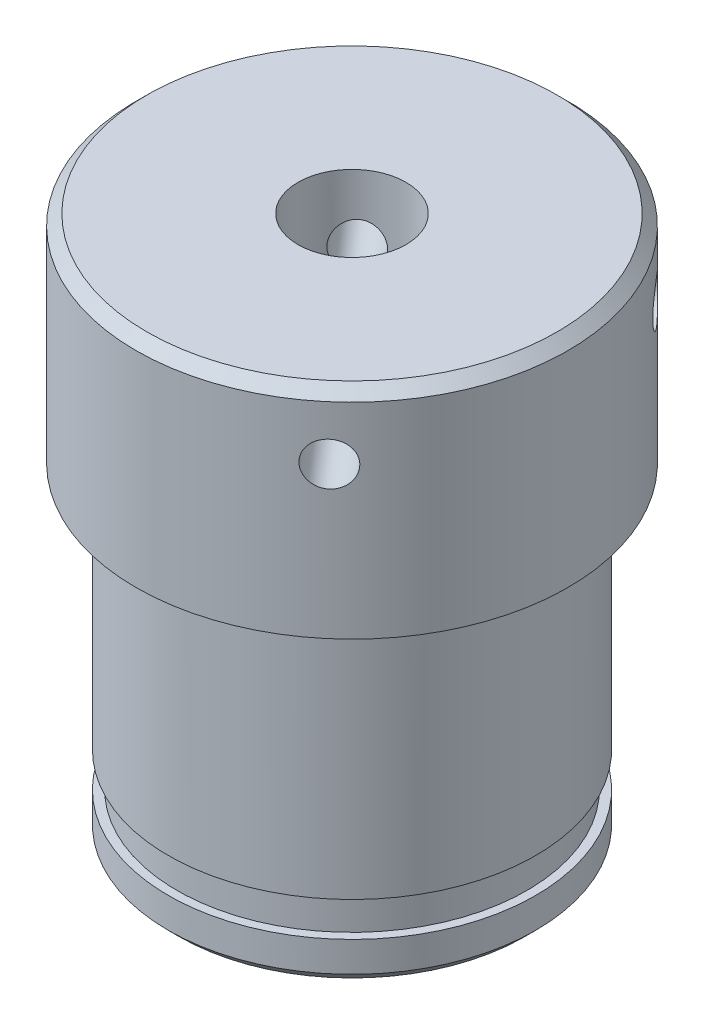
SolidWorks part; units mm, degrees
material "1060 Сплав"
ref_plane "Спереди" through (0, 0, 0) normal (0, 0, 1) x (1, 0, 0)
ref_plane "Сверху" through (0, 0, 0) normal (0, 1, 0) x (1, 0, 0)
ref_plane "Справа" through (0, 0, 0) normal (1, 0, 0) x (0, 0, -1)
sketch "Эскиз1" plane through (0, 0, 0) normal (0, 1, 0) x (1, 0, 0)
  circle A0 centre (0, 0) radius 8.5
  dimension "D1" = 17
extrude "Бобышка-Вытянуть1" add sketch "Эскиз1" along normal blind 15
sketch "Эскиз2" plane through (0, 15, 0) normal (0, 1, 0) x (1, 0, 0)
  circle A0 centre (0, 0) radius 10
  dimension "D1" = 20
extrude "Бобышка-Вытянуть2" add sketch "Эскиз2" along normal blind 10
sketch "Эскиз3" plane through (0, 0, 0) normal (0, -1, 0) x (1, 0, 0)
  circle A0 centre (0, 6) radius 1
  circle A1 centre (6, 0) radius 1
  circle A2 centre (0, -6) radius 1
  circle A3 centre (-6, 0) radius 1
  point P12 (0, 0)
  dimension "D1" = 2
  dimension "D2" = 6
  dimension "D3" = 4
extrude "Вырез-Вытянуть1" cut sketch "Эскиз3" against normal blind 10
sketch "Эскиз4" plane through (0, 0, 0) normal (0, -1, 0) x (1, 0, 0)
  circle A0 centre (0, 0) radius 8.1
  circle A1 centre (0, 0) radius 8.5
  dimension "D1" = 16.2
extrude "Вырез-Вытянуть2" cut sketch "Эскиз4" against normal blind 1.6 from offset 1.9 offset against normal yes
chamfer "Фаска1" distance 0.5 angle 45 2 edges at (0, 0, 8.5) (0, 25, 10)
sketch "Эскиз6" plane through (0, 25, 0) normal (0, 1, 0) x (1, 0, 0)
  line L0 (0, 12.2337) -> (0, -13.1957) construction
ref_plane "Плоскость1" through (6.5246, 0, 7.5782) normal (0.6525, 0, 0.7578) x (0.7578, 0, -0.6525)
sketch "Эскиз7" plane through (6.5246, 0, 7.5782) normal (0.6525, 0, 0.7578) x (0.7578, 0, -0.6525)
  line L0 (7.982, 25) -> (-8.6096, 25) construction
  circle A0 centre (0, 22) radius 1
  dimension "D1" = 2
  dimension "D2" = 3
extrude "Вырез-Вытянуть3" cut sketch "Эскиз7" against normal blind 8
pattern_circular "Круговой массив1" count 4 over 360 about axis through (0, 0, 0) along (0, 1, 0) of "Вырез-Вытянуть3"
sketch "Эскиз8" plane through (0, 0, 0) normal (0, -1, 0) x (1, 0, 0)
  circle A0 centre (0, 0) radius 3.5
  dimension "D1" = 7
extrude "Вырез-Вытянуть4" cut sketch "Эскиз8" against normal blind 5.5
chamfer "Фаска2" distance 0.5 angle 45 1 edges at (0, 0, -3.5)
sketch "Эскиз9" plane through (0, 5.5, 0) normal (0, -1, 0) x (1, 0, 0)
  circle A0 centre (0, 0) radius 2.5
  dimension "D1" = 5
extrude "Вырез-Вытянуть5" cut sketch "Эскиз9" against normal up to next
